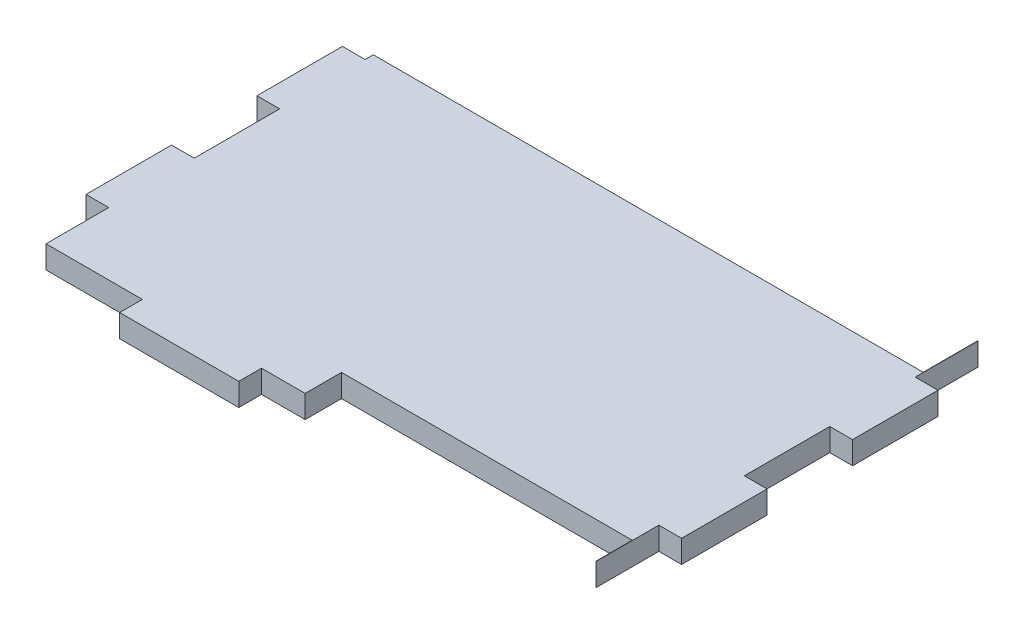
SolidWorks part; units mm, degrees
ref_plane "Front Plane" through (0, 0, 0) normal (0, 0, 1) x (1, 0, 0)
ref_plane "Top Plane" through (0, 0, 0) normal (0, 1, 0) x (1, 0, 0)
ref_plane "Right Plane" through (0, 0, 0) normal (1, 0, 0) x (0, 0, -1)
sketch "Sketch1" plane through (0, 0, 0) normal (0, 1, 0) x (1, 0, 0)
  line L1 (-41.5925, -29.845) -> (41.5925, -29.845)
  line L2 (-41.5925, -29.845) -> (-41.5925, 29.845)
  line L3 (-41.5925, 29.845) -> (41.5925, 29.845)
  line L4 (41.5925, -29.845) -> (41.5925, 29.845)
  line L5 (-41.5925, -29.845) -> (41.5925, 29.845) construction
  line L6 (-41.5925, 29.845) -> (41.5925, -29.845) construction
  point P0 (0, 0)
  dimension "D1" = 83.185
  dimension "D2" = 59.69
extrude "Boss-Extrude1" add sketch "Sketch1" along normal blind 3.175
sketch "Sketch2" plane through (0, 3.175, 0) normal (0, 1, 0) x (1, 0, 0)
  line L1 (-41.5925, 29.845) -> (-24.9555, 29.845)
  line L2 (-41.5925, 29.845) -> (-41.5925, 26.67)
  line L3 (-41.5925, 26.67) -> (-24.9555, 26.67)
  line L4 (-24.9555, 29.845) -> (-24.9555, 26.67)
  line L5 (-41.5925, -29.845) -> (-24.9555, -29.845)
  line L6 (-41.5925, -29.845) -> (-41.5925, -26.67)
  line L7 (-41.5925, -26.67) -> (-24.9555, -26.67)
  line L8 (-24.9555, -29.845) -> (-24.9555, -26.67)
  dimension "D1" = 16.637
  dimension "D2" = 3.175
  dimension "D3" = 3.175
extrude "Cut-Extrude1" cut sketch "Sketch2" against normal blind 3.175
pattern_linear "LPattern1" count 3 spacing 33.274 along (1, 0, 0) of "Cut-Extrude1"
sketch "Sketch3" plane through (0, 3.175, 0) normal (0, 1, 0) x (1, 0, 0)
  line L1 (-41.5925, -29.845) -> (41.5925, -29.845) construction
  line L2 (-41.5925, -29.845) -> (-41.5925, 29.845) construction
  line L3 (-41.5925, 29.845) -> (41.5925, 29.845) construction
  line L4 (41.5925, -29.845) -> (41.5925, 29.845) construction
  line L5 (-41.5925, -29.845) -> (41.5925, 29.845) construction
  line L6 (-41.5925, 29.845) -> (41.5925, -29.845) construction
  line L7 (-41.5925, 29.845) -> (-38.4175, 29.845)
  line L8 (-41.5925, 29.845) -> (-41.5925, 17.907)
  line L9 (-41.5925, 17.907) -> (-38.4175, 17.907)
  line L10 (-38.4175, 29.845) -> (-38.4175, 17.907)
  line L11 (41.5925, 29.845) -> (38.4175, 29.845)
  line L12 (41.5925, 29.845) -> (41.5925, 17.907)
  line L13 (41.5925, 17.907) -> (38.4175, 17.907)
  line L14 (38.4175, 29.845) -> (38.4175, 17.907)
  point P0 (0, 0)
  dimension "D1" = 83.185
  dimension "D2" = 59.69
  dimension "D3" = 3.175
  dimension "D4" = 11.938
  dimension "D5" = 3.175
extrude "Cut-Extrude2" cut sketch "Sketch3" against normal blind 3.175
pattern_linear "LPattern4" count 3 spacing 23.876 along (0, 0, 1) of "Cut-Extrude2"
sketch "Sketch4" plane through (0, 3.175, 0) normal (0, 1, 0) x (1, 0, 0)
  line L0 (-24.9555, 26.67) -> (24.9555, 26.67)
  line L1 (-38.4175, -26.67) -> (38.4175, -26.67) construction
  line L2 (-38.4175, -26.67) -> (-38.4175, 26.67) construction
  line L3 (-38.4175, 26.67) -> (38.4175, 26.67) construction
  line L4 (38.4175, -26.67) -> (38.4175, 26.67) construction
  line L5 (-38.4175, -26.67) -> (38.4175, 26.67) construction
  line L6 (-38.4175, 26.67) -> (38.4175, -26.67) construction
  line L7 (24.9555, 26.67) -> (24.9555, 29.845)
  line L8 (24.9555, 29.845) -> (-24.9555, 29.845)
  line L9 (-24.9555, 29.845) -> (-24.9555, 26.67)
  line L10 (-24.9555, -26.67) -> (-24.9555, -29.845)
  line L11 (-24.9555, -29.845) -> (24.9555, -29.845)
  line L12 (24.9555, -29.845) -> (24.9555, -26.67)
  line L13 (24.9555, -26.67) -> (-24.9555, -26.67)
  line L14 (-38.4175, 26.67) -> (-38.4175, 19.05)
  line L15 (-38.4175, 26.67) -> (38.4175, 26.67)
  line L16 (38.4175, 26.67) -> (38.4175, 19.05)
  line L17 (38.4175, 19.05) -> (-38.4175, 19.05)
  line L18 (38.4175, -26.67) -> (38.4175, -21.59)
  line L19 (38.4175, -21.59) -> (-2.2225, -21.59)
  line L20 (-2.2225, -21.59) -> (-2.2225, -26.67)
  line L21 (-2.2225, -26.67) -> (38.4175, -26.67)
  point P0 (0, 0)
  dimension "D1" = 76.835
  dimension "D2" = 53.34
sketch "Sketch5" plane through (0, 3.175, 0) normal (0, 1, 0) x (1, 0, 0)
  line L2 (-38.4175, 19.05) -> (38.3841, 19.05)
  line L3 (-38.4175, 19.05) -> (-38.4175, 30.2541)
  line L4 (-38.4175, 30.2541) -> (38.3841, 30.2541)
  line L5 (38.3841, 19.05) -> (38.3841, 30.2541)
  line L6 (-2.2225, -21.59) -> (38.3841, -21.59)
  line L7 (-2.2225, -21.59) -> (-2.2225, -34.6079)
  line L8 (-2.2225, -34.6079) -> (38.3841, -34.6079)
  line L9 (38.3841, -21.59) -> (38.3841, -34.6079)
extrude "Cut-Extrude4" cut sketch "Sketch5" against normal blind 3.175
